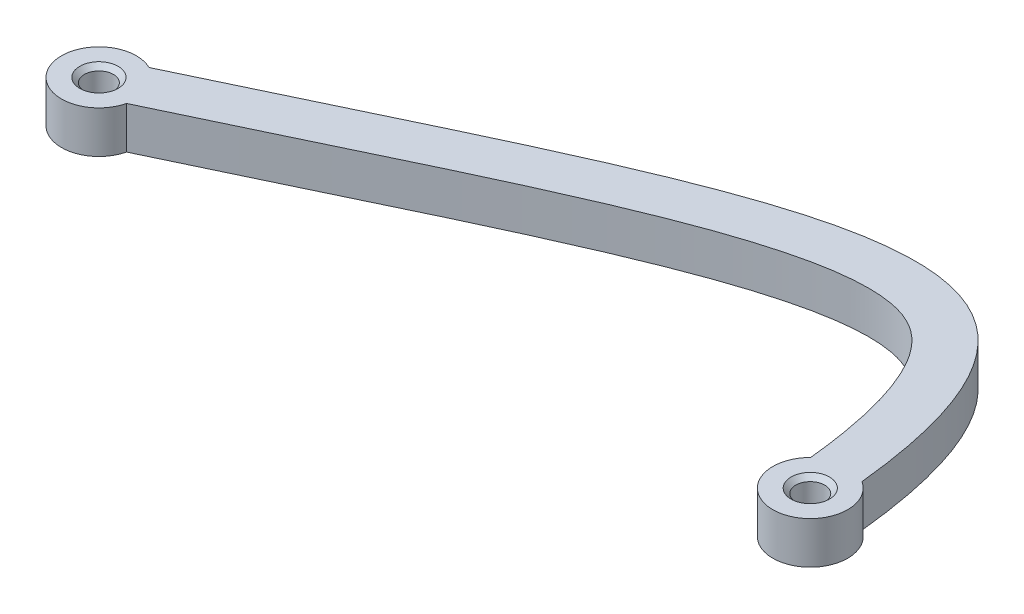
SolidWorks part; units mm, degrees
ref_plane "Front Plane" through (0, 0, 0) normal (0, 0, 1) x (1, 0, 0)
ref_plane "Top Plane" through (0, 0, 0) normal (0, 1, 0) x (1, 0, 0)
ref_plane "Right Plane" through (0, 0, 0) normal (1, 0, 0) x (0, 0, -1)
sketch "Sketch3" plane through (0, 0, 0) normal (0, 1, 0) x (1, 0, 0)
  arc A12 (-2.8082, 2.8485) -> (2.1652, 3.3633) centre (0, 0) ccw
  arc A13 (-74.2351, 3.5896) -> (-72.1113, -0.937) centre (-76, 0) ccw
  circle A14 centre (-76, 0) radius 1.55
  circle A15 centre (0, 0) radius 1.55
  spline S0 degree 3 poles (-74.2351, 3.5896) (-27.4855, 25.5238) (-1.8428, 42.0826) (2.1652, 3.3633) knots 0 0 0 0 1 1 1 1
  spline S1 degree 1 poles (-72.1113, -0.937) (-2.8082, 2.8485) knots 0 0 1 1 construction
  spline S2 degree 3 poles (-72.1113, -0.937) (-71.3821, -0.5948) (-69.9173, 0.0947) (-67.0492, 1.4521) (-63.5397, 3.1244) (-59.4624, 5.0765) (-54.2014, 7.5959) (-47.9584, 10.564) (-41.0092, 13.76) (-34.6176, 16.5131) (-26.8715, 19.4962) (-20.3514, 21.2888) (-15.317, 21.7237) (-12.3561, 21.4252) (-10.1448, 20.6312) (-8.3382, 19.3505) (-6.6114, 17.2312) (-5.2679, 14.4529) (-4.3327, 11.5464) (-3.717, 9.0215) (-3.2853, 6.6177) (-2.995, 4.5314) (-2.8656, 3.403) (-2.8082, 2.8485) knots 0 0 0 0 0.015625 0.03125 0.0625 0.09375 0.125 0.1875 0.25 0.3125 0.375 0.5 0.5625 0.625 0.6875 0.75 0.8125 0.875 0.90625 0.9375 0.96875 0.984375 1 1 1 1
  point P5 (0, 0)
  dimension "D1" = 76
  dimension "D3" = 3.1
  dimension "D8" = 8
  dimension "D2" = 5
extrude "Boss-Extrude1" add sketch "Sketch3" along normal mid plane 4.5
chamfer "Chamfer1" distance 0.5 angle 45
